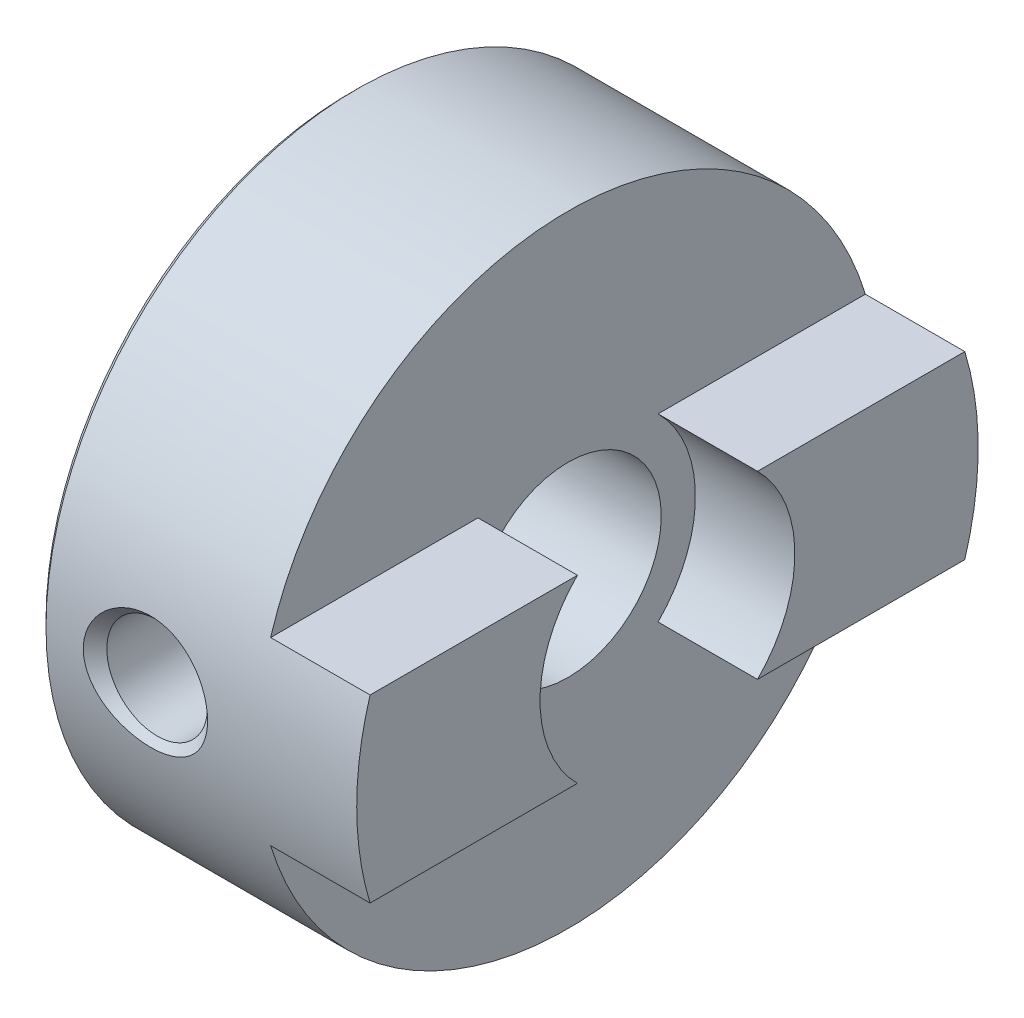
SolidWorks part; units mm, degrees
ref_plane "Front Plane" through (0, 0, 0) normal (0, 0, 1) x (1, 0, 0)
ref_plane "Top Plane" through (0, 0, 0) normal (0, 1, 0) x (1, 0, 0)
ref_plane "Right Plane" through (0, 0, 0) normal (1, 0, 0) x (0, 0, -1)
ref_plane "Plane1" through (0, 0, 0) normal (0, 0, 1) x (1, 0, 0)
sketch "Sketch1" plane through (0, 0, 0) normal (0, 0, 1) x (1, 0, 0)
  line L0 (0, 9.8) -> (0, 3)
  line L1 (0, 3) -> (10.2, 3)
  line L2 (10.2, 3) -> (10.2, 10)
  line L3 (10.2, 10) -> (0.2, 10)
  line L4 (0.2, 10) -> (0, 9.8)
  line L5 (10.2, 0) -> (0, 0) construction
revolve "Revolve1" add sketch "Sketch1" angle 360 about L5
ref_plane "Plane2" through (0, 0, 0) normal (0, 0, 1) x (1, 0, 0)
sketch "Sketch2" plane through (0, 0, 0) normal (0, 0, 1) x (1, 0, 0)
  line L0 (7, 0) -> (7, 4.1)
  line L1 (7, 4.1) -> (10.2, 4.1)
  line L2 (10.2, 4.1) -> (10.2, 0)
  line L3 (10.2, 0) -> (7, 0)
  line L4 (10.2, 0) -> (7, 0) construction
revolve "Cut-Revolve1" cut sketch "Sketch2" angle 360 about L4
ref_plane "Plane3" through (10.2, 0, 0) normal (1, 0, 0) x (0, 0, -1)
sketch "Sketch3" plane through (10.2, 0, 0) normal (1, 0, 0) x (0, 0, -1)
  line L0 (-11, 10.5) -> (-11, -10.5)
  line L1 (-11, -10.5) -> (11, -10.5)
  line L2 (11, -10.5) -> (11, 10.5)
  line L3 (11, 10.5) -> (-11, 10.5)
  line L4 (-10, 2.9) -> (-10, -2.9)
  line L5 (-10, -2.9) -> (10, -2.9)
  line L6 (10, -2.9) -> (10, 2.9)
  line L7 (10, 2.9) -> (-10, 2.9)
extrude "Cut-Extrude1" cut sketch "Sketch3" against normal blind 3.2
ref_plane "Plane4" through (3.4, 0, 0) normal (1, 0, 0) x (0, 0, -1)
sketch "Sketch4" plane through (3.4, 0, 0) normal (1, 0, 0) x (0, 0, -1)
  line L0 (-10, 0) -> (-10, 2)
  line L1 (-10, 2) -> (-9.621, 1.621)
  line L2 (-9.621, 1.621) -> (0, 1.621)
  line L3 (0, 1.621) -> (0, 0)
  line L4 (0, 0) -> (-10, 0)
  line L5 (0, 0) -> (-10, 0) construction
revolve "Cut-Revolve2" cut sketch "Sketch4" angle 360 about L5
ref_plane "Plane5" through (3.4, 0, 0) normal (1, 0, 0) x (0, 0, -1)
sketch "Sketch5" plane through (3.4, 0, 0) normal (1, 0, 0) x (0, 0, -1)
  line L0 (0, -10) -> (-2, -10)
  line L1 (-2, -10) -> (-1.621, -9.621)
  line L2 (-1.621, -9.621) -> (-1.621, 0)
  line L3 (-1.621, 0) -> (0, 0)
  line L4 (0, 0) -> (0, -10)
  line L5 (0, 0) -> (0, -10) construction
revolve "Cut-Revolve3" cut sketch "Sketch5" angle 360 about L5
